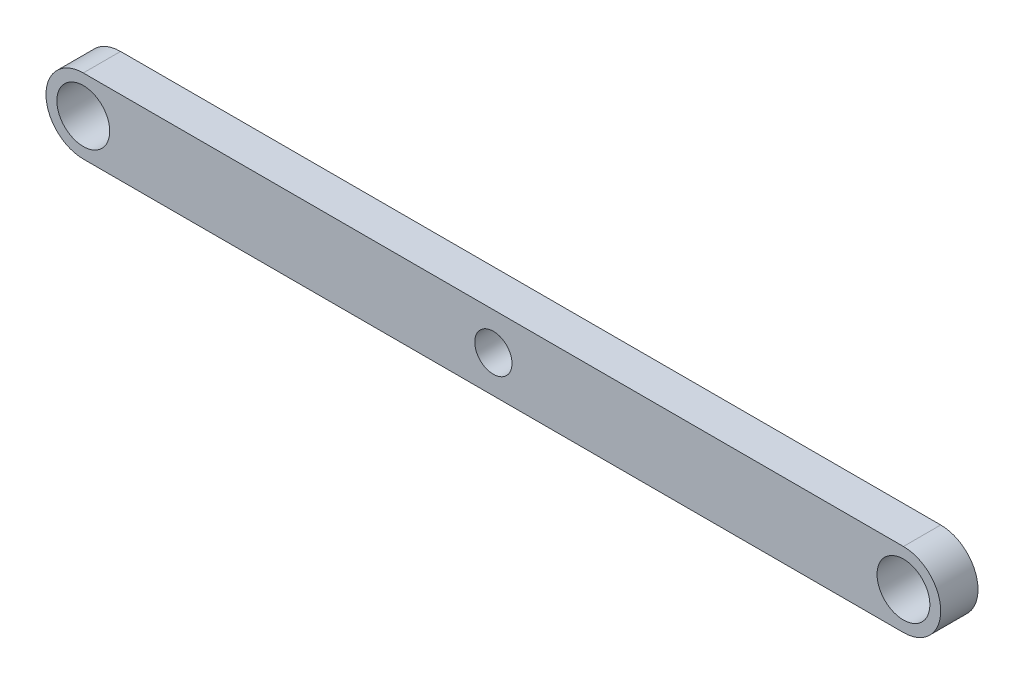
SolidWorks part; units mm, degrees
ref_plane "Front Plane" through (0, 0, 0) normal (0, 0, 1) x (1, 0, 0)
ref_plane "Top Plane" through (0, 0, 0) normal (0, 1, 0) x (1, 0, 0)
ref_plane "Right Plane" through (0, 0, 0) normal (1, 0, 0) x (0, 0, -1)
sketch "Sketch1" plane through (0, 0, 0) normal (0, 0, 1) x (1, 0, 0)
  line L0 (-69.85, 0) -> (69.85, 0) construction
  line L1 (-69.85, 6.35) -> (69.85, 6.35)
  line L2 (-69.85, -6.35) -> (69.85, -6.35)
  arc A0 (-69.85, 6.35) -> (-69.85, -6.35) centre (-69.85, 0) ccw
  arc A1 (69.85, -6.35) -> (69.85, 6.35) centre (69.85, 0) ccw
  circle A2 centre (-69.85, 0) radius 4.5
  circle A3 centre (69.85, 0) radius 4.5
  circle A4 centre (0, 0) radius 3.175
  point P2 (0, 0)
  dimension "D3" = 9
  dimension "D4" = 6.35
  dimension "D1" = 139.7
  dimension "D2" = 12.7
extrude "Boss-Extrude1" add sketch "Sketch1" along normal blind 6.35
